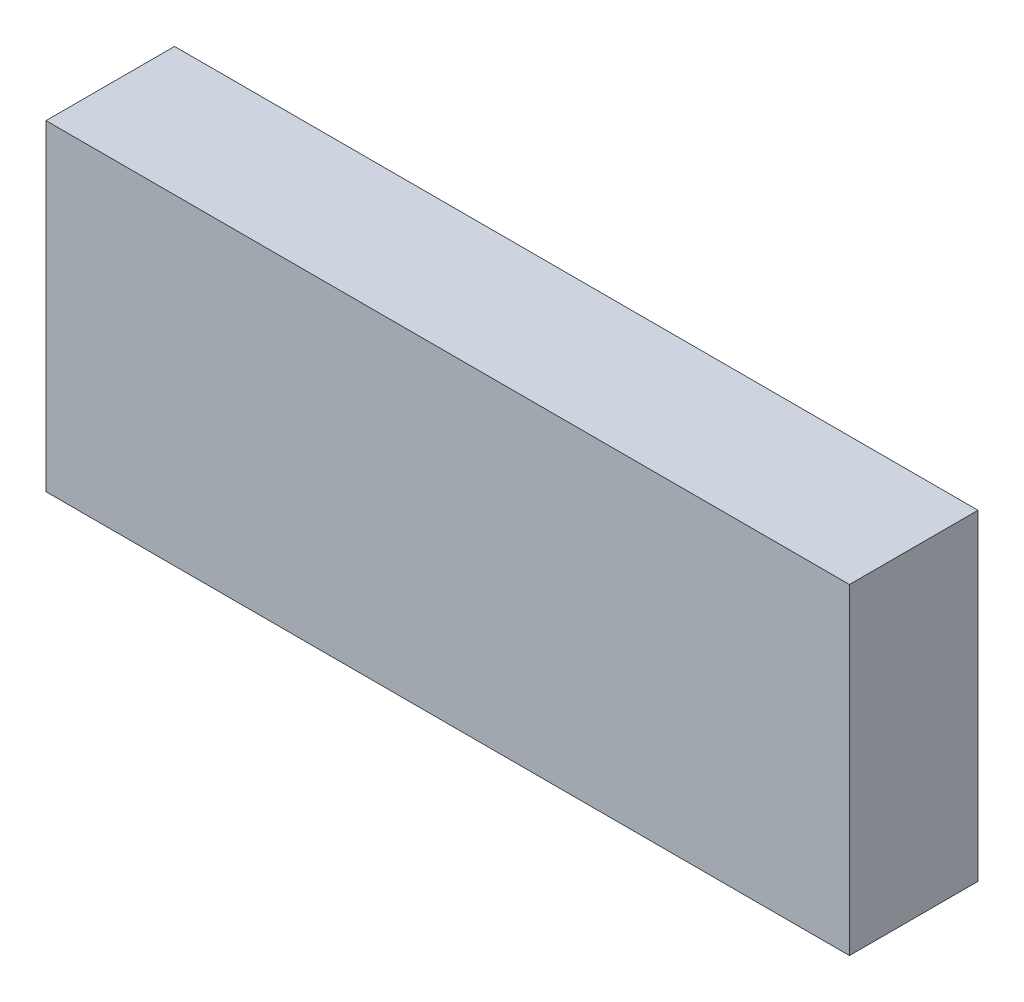
SolidWorks part; units mm, degrees
ref_plane "Front Plane" through (0, 0, 0) normal (0, 0, 1) x (1, 0, 0)
ref_plane "Top Plane" through (0, 0, 0) normal (0, 1, 0) x (1, 0, 0)
ref_plane "Right Plane" through (0, 0, 0) normal (1, 0, 0) x (0, 0, -1)
sketch "Sketch1" plane through (0, 0, 0) normal (0, 0, 1) x (1, 0, 0)
  line L1 (12.5, -5) -> (-12.5, -5)
  line L2 (12.5, -5) -> (12.5, 5)
  line L3 (12.5, 5) -> (-12.5, 5)
  line L4 (-12.5, -5) -> (-12.5, 5)
  line L5 (12.5, -5) -> (-12.5, 5) construction
  line L6 (12.5, 5) -> (-12.5, -5) construction
  point P0 (0, 0)
  dimension "D1" = 25
  dimension "D2" = 10
extrude "Boss-Extrude1" add sketch "Sketch1" along normal blind 4
